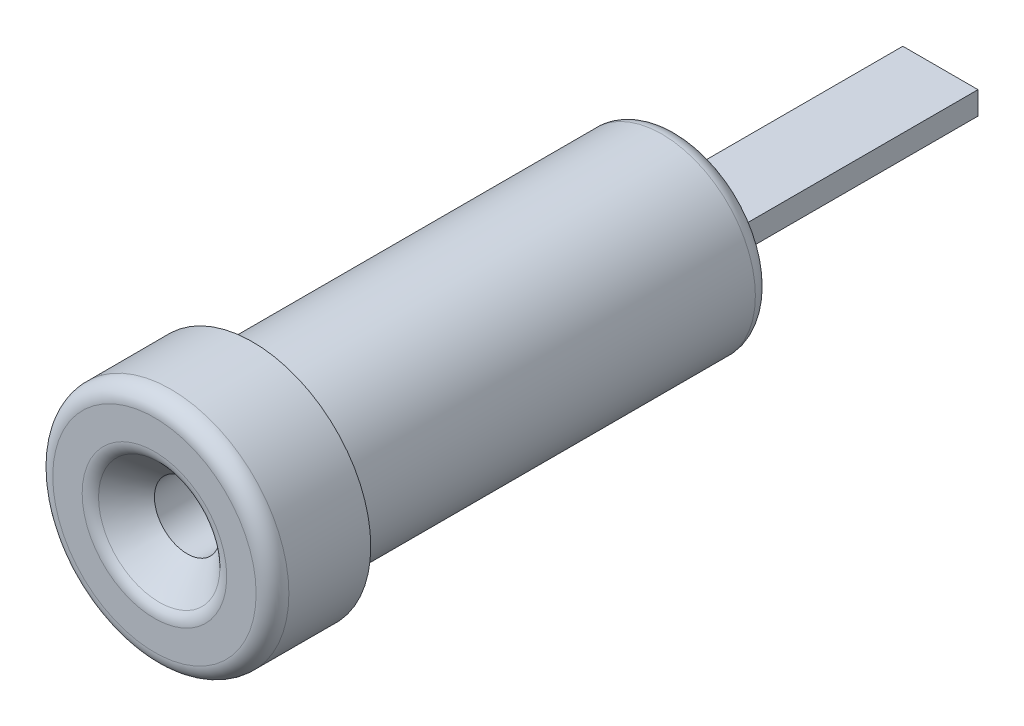
SolidWorks part; units mm, degrees
ref_plane "Front Plane" through (0, 0, 0) normal (0, 0, 1) x (1, 0, 0)
ref_plane "Top Plane" through (0, 0, 0) normal (0, 1, 0) x (1, 0, 0)
ref_plane "Right Plane" through (0, 0, 0) normal (1, 0, 0) x (0, 0, -1)
sketch "Sketch2" plane through (0, 0, 0) normal (1, 0, 0) x (0, 0, -1)
  line L0 (0, 0) -> (66.0385, 0) construction
  line L1 (0, 1) -> (12, 1)
  line L2 (12, 1) -> (12, 0)
  line L3 (12, 0) -> (24, 0)
  line L4 (24, 0) -> (24, 1.2)
  line L5 (24, 1.2) -> (16, 1.2)
  line L6 (16, 1.2) -> (16, 2.85)
  line L7 (16, 2.85) -> (3, 2.85)
  line L8 (3, 2.85) -> (3, 3.605)
  line L9 (3, 3.605) -> (0, 3.605)
  line L10 (0, 3.605) -> (0, 1)
  dimension "D1" = 2
  dimension "D2" = 12
  dimension "D3" = 24
  dimension "D4" = 8
  dimension "D5" = 5.7
  dimension "D6" = 2.4
  dimension "D7" = 7.21
  dimension "D8" = 3
revolve "Revolve1" add sketch "Sketch2" angle 360 about L0
sketch "Sketch3" plane through (0, 0, -24) normal (0, 0, -1) x (-1, 0, 0)
  line L1 (-1.1478, 0.35) -> (1.1478, 0.35)
  line L2 (-1.1478, 0.35) -> (-1.1478, -0.35)
  line L3 (-1.1478, -0.35) -> (1.1478, -0.35)
  line L4 (1.1478, 0.35) -> (1.1478, -0.35)
  line L5 (-1.1478, 0.35) -> (1.1478, -0.35) construction
  line L6 (-1.1478, -0.35) -> (1.1478, 0.35) construction
  line L7 (-2.0153, -2.0153) -> (2.0153, -2.0153)
  line L8 (-2.0153, -2.0153) -> (-2.0153, 2.0153)
  line L9 (-2.0153, 2.0153) -> (2.0153, 2.0153)
  line L10 (2.0153, -2.0153) -> (2.0153, 2.0153)
  line L11 (-2.0153, -2.0153) -> (2.0153, 2.0153) construction
  line L12 (-2.0153, 2.0153) -> (2.0153, -2.0153) construction
  circle A1 centre (0, 0) radius 1.2 construction
  circle A2 centre (0, 0) radius 2.85 construction
  point P0 (0, 0)
  point P7 (0, 0)
  dimension "D1" = 0.7
extrude "Cut-Extrude1" cut sketch "Sketch3" against normal up to surface (8 mm away) up to face at (2.85, 0, -16)
chamfer "Chamfer1" distance 1 angle 45 1 edges at (1, 0, 0)
fillet "Fillet1" radius 0.5 3 edges at (3.605, 0, 0) (-2, 0, 0) (2.85, 0, -16)
